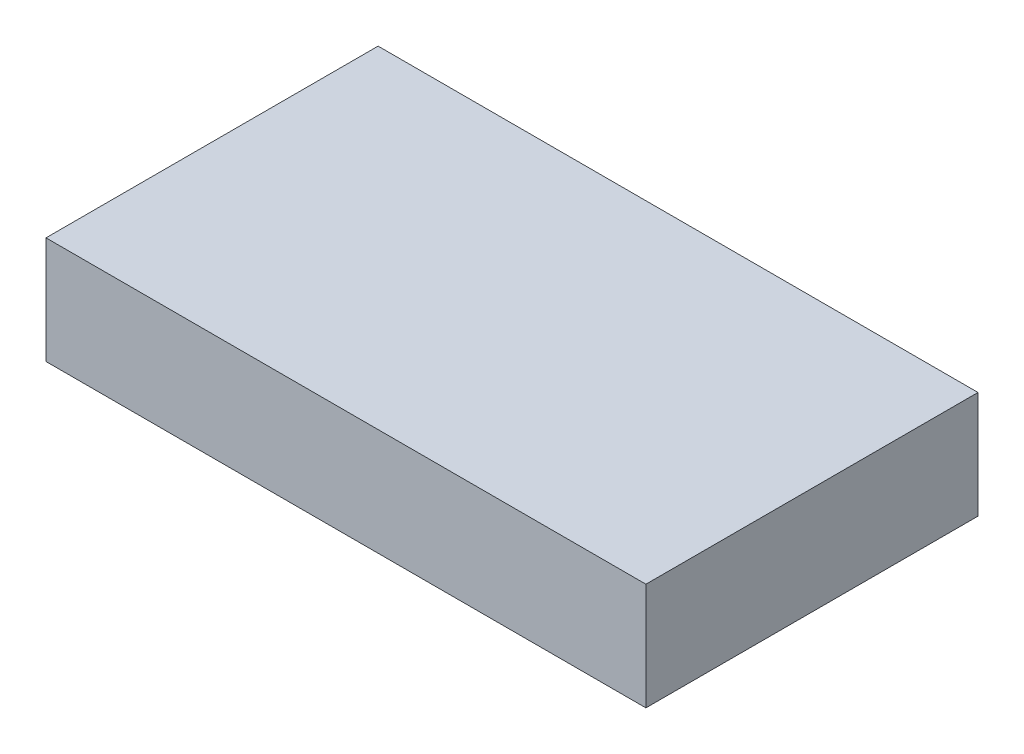
SolidWorks part; units mm, degrees
ref_plane "Front Plane" through (0, 0, 0) normal (0, 0, 1) x (1, 0, 0)
ref_plane "Top Plane" through (0, 0, 0) normal (0, 1, 0) x (1, 0, 0)
ref_plane "Right Plane" through (0, 0, 0) normal (1, 0, 0) x (0, 0, -1)
sketch "Sketch1" plane through (0, 0, 0) normal (0, 1, 0) x (1, 0, 0)
  line L1 (-28, -15.5) -> (28, -15.5)
  line L2 (-28, -15.5) -> (-28, 15.5)
  line L3 (-28, 15.5) -> (28, 15.5)
  line L4 (28, -15.5) -> (28, 15.5)
  line L5 (-28, -15.5) -> (28, 15.5) construction
  line L6 (-28, 15.5) -> (28, -15.5) construction
  point P0 (0, 0)
  dimension "D1" = 31
  dimension "D2" = 56
extrude "Boss-Extrude1" add sketch "Sketch1" along normal blind 10
